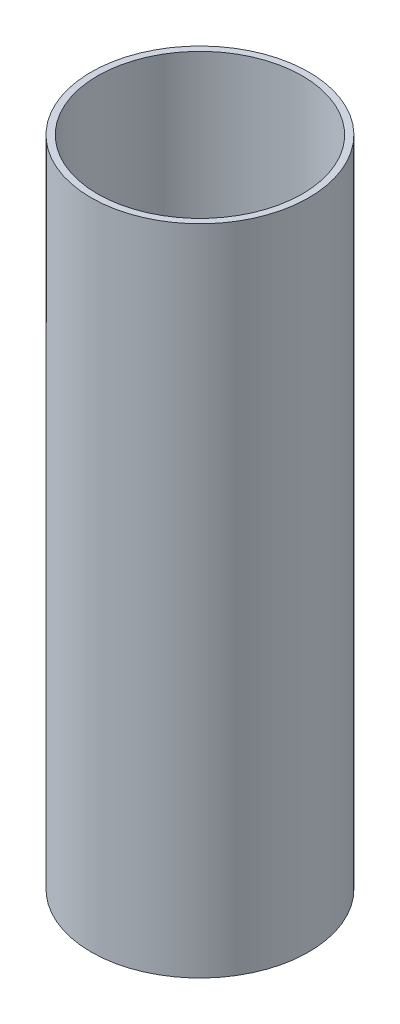
SolidWorks part; units mm, degrees
ref_plane "Front Plane" through (0, 0, 0) normal (0, 0, 1) x (1, 0, 0)
ref_plane "Top Plane" through (0, 0, 0) normal (0, 1, 0) x (1, 0, 0)
ref_plane "Right Plane" through (0, 0, 0) normal (1, 0, 0) x (0, 0, -1)
sketch "Sketch1" plane through (0, 0, 0) normal (0, 1, 0) x (1, 0, 0)
  circle A0 centre (0, 0) radius 6.35
  circle A1 centre (0, 0) radius 5.969
  dimension "D1" = 12.7
  dimension "D2" = 11.938
sketch "Sketch2" plane through (0, 0, 0) normal (1, 0, 0) x (0, 0, -1)
  line L0 (0, 0) -> (0, 38.1)
  dimension "D1" = 38.1
sweep "Sweep1" add profiles "Sketch1" path "Sketch2"
